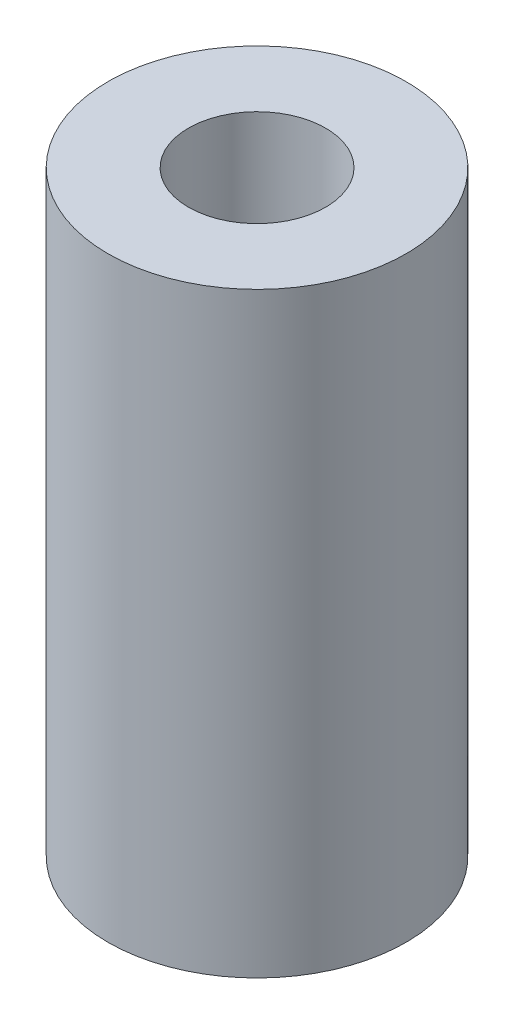
SolidWorks part; units mm, degrees
ref_plane "Plan de face" through (0, 0, 0) normal (0, 0, 1) x (1, 0, 0)
ref_plane "Plan de dessus" through (0, 0, 0) normal (0, 1, 0) x (1, 0, 0)
ref_plane "Plan de droite" through (0, 0, 0) normal (1, 0, 0) x (0, 0, -1)
sketch "Sketch1" plane through (0, 0, 0) normal (0, 1, 0) x (1, 0, 0)
  circle A0 centre (0, 0) radius 2.5
  dimension "D1" = 5
extrude "Boss-Extrude1" add sketch "Sketch1" along normal blind 10 contours A0
sketch "Sketch2" plane through (0, 10, 0) normal (0, 1, 0) x (1, 0, 0)
  circle A0 centre (0, 0) radius 1.15
  dimension "D1" = 2.3
extrude "Cut-Extrude1" cut sketch "Sketch2" against normal blind 8
